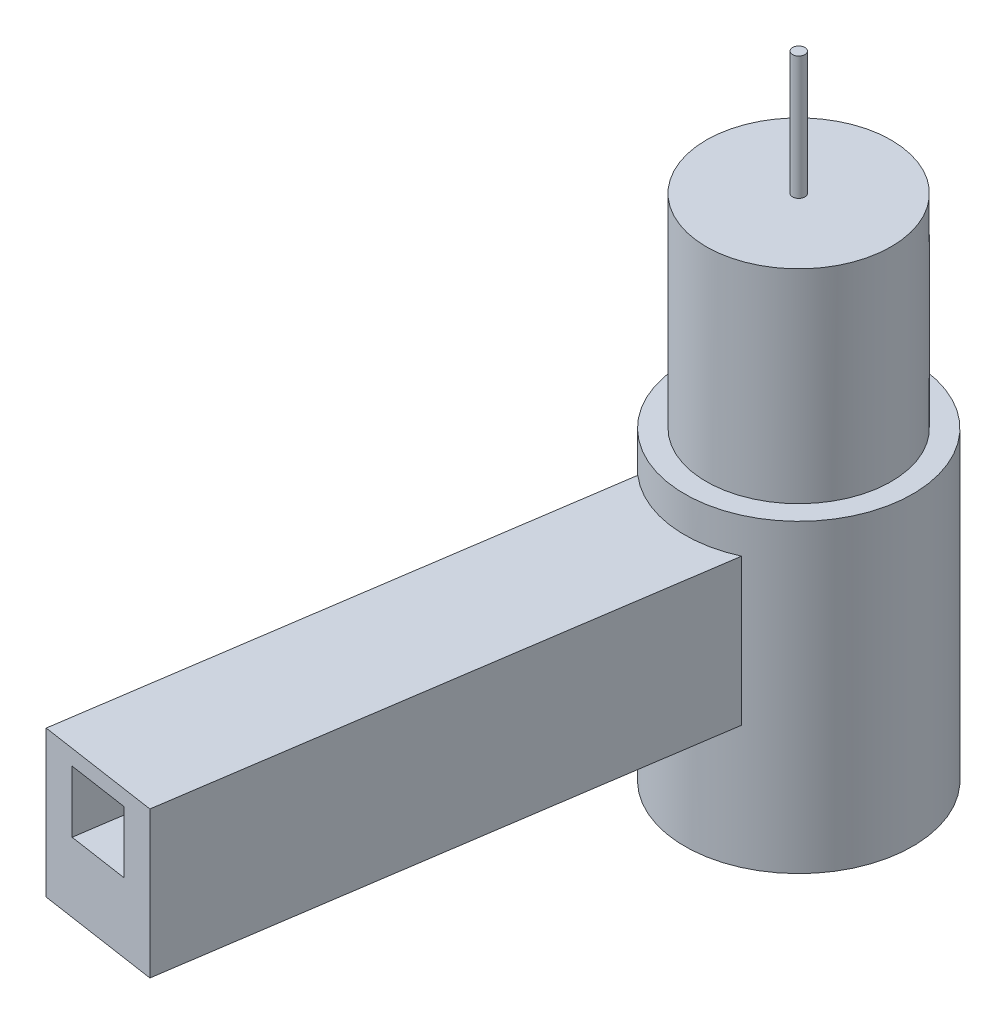
SolidWorks part; units mm, degrees
ref_plane "Front Plane" through (0, 0, 0) normal (0, 0, 1) x (1, 0, 0)
ref_plane "Top Plane" through (0, 0, 0) normal (0, 1, 0) x (1, 0, 0)
ref_plane "Right Plane" through (0, 0, 0) normal (1, 0, 0) x (0, 0, -1)
sketch "Sketch1" plane through (0, 0, 0) normal (0, 1, 0) x (1, 0, 0)
  circle A0 centre (0, 0) radius 3
  dimension "D1" = 6
extrude "Boss-Extrude1" add sketch "Sketch1" along normal blind 16.5
sketch "Sketch2" plane through (0, 0, 0) normal (0, -1, 0) x (1, 0, 0)
  circle A0 centre (0, 0) radius 3.7
  dimension "D1" = 7.4
extrude "Boss-Extrude2" add sketch "Sketch2" against normal blind 9.9
sketch "Sketch3" plane through (0, 0, 0) normal (0, -1, 0) x (1, 0, 0)
  line L0 (-0.5469, 3.6594) -> (-2.956, 19.7803) construction
  line L1 (-2.4381, 2.7831) -> (-4.934, 19.4847)
  line L2 (1.518, 3.3743) -> (-0.978, 20.0759)
  line L3 (-4.934, 19.4847) -> (-0.978, 20.0759)
  line L4 (-1.978, -0.2956) -> (-4.934, 19.4847) construction
  line L5 (0, 0) -> (-2.956, 19.7803) construction
  line L6 (1.978, 0.2956) -> (-0.978, 20.0759) construction
  arc A0 (1.518, 3.3743) -> (-2.4381, 2.7831) centre (0, 0) ccw
  dimension "D3" = 20
  dimension "D1" = 2
  dimension "D2" = 2
extrude "Boss-Extrude3" add sketch "Sketch3" along normal blind 4.75 from offset 8.75 offset against normal yes
sketch "Sketch4" plane through (0, 16.5, 0) normal (0, 1, 0) x (1, 0, 0)
  circle A0 centre (0, 0) radius 0.2
extrude "Boss-Extrude4" add sketch "Sketch4" along normal blind 4
sketch "Sketch5" plane through (-2.956, 0, 19.7803) normal (-0.1478, 0, 0.989) x (0.989, 0, 0.1478)
  line L0 (-2, 8.75) -> (2, 8.75) construction
  line L1 (-2, 8.25) -> (2, 8.25)
  line L2 (-2, 6.25) -> (2, 6.25)
  line L3 (0, 8.25) -> (0, 6.25) construction
  line L4 (-1, 8.25) -> (-1, 6.25)
  line L5 (1, 8.25) -> (1, 6.25)
  dimension "D1" = 0.5
  dimension "D2" = 2
  dimension "D3" = 1
  dimension "D4" = 1
extrude "Cut-Extrude1" cut sketch "Sketch5" against normal blind 20 from surface at 0 contours L5 L1 L4 L2 starting at face at (-2.956, 6.375, 19.7803)
